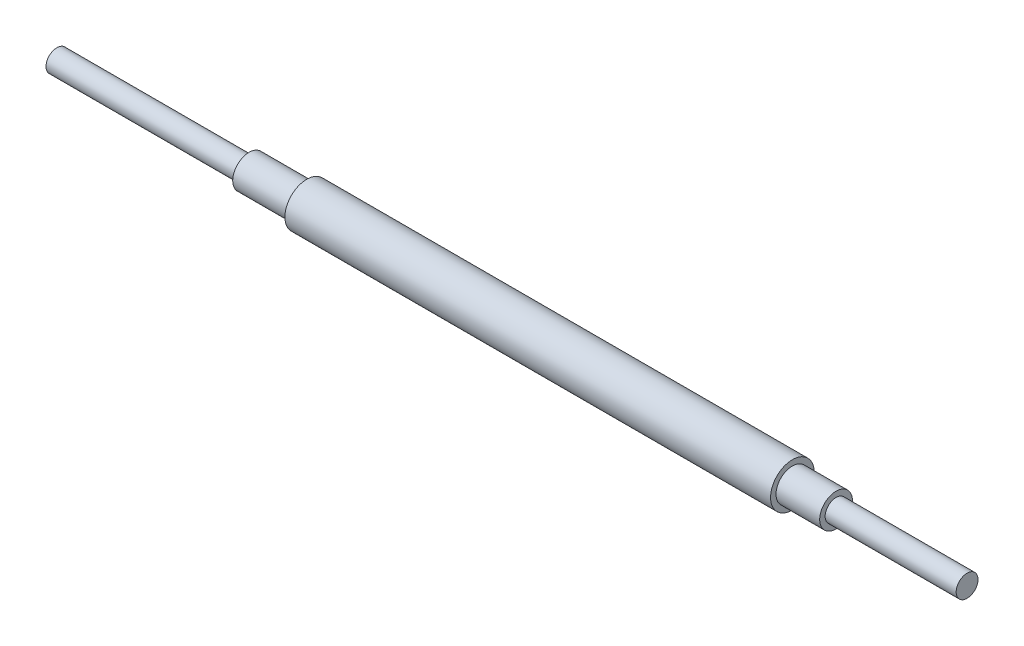
SolidWorks part; units mm, degrees
ref_plane "Front Plane" through (0, 0, 0) normal (0, 0, 1) x (1, 0, 0)
ref_plane "Top Plane" through (0, 0, 0) normal (0, 1, 0) x (1, 0, 0)
ref_plane "Right Plane" through (0, 0, 0) normal (1, 0, 0) x (0, 0, -1)
sketch "Sketch1" plane through (0, 0, 0) normal (0, 0, 1) x (1, 0, 0)
  line L3 (0.6124, 3.175) -> (0.6124, 0)
  line L4 (0.6124, 3.175) -> (-37.4876, 3.175)
  line L5 (-37.4876, 3.175) -> (-37.4876, 4.7625)
  line L6 (-37.4876, 4.7625) -> (-50.1876, 4.7625)
  line L7 (-50.1876, 4.7625) -> (-50.1876, 6.35)
  line L8 (-50.1876, 6.35) -> (-191.4116, 6.35)
  line L9 (-191.4116, 6.35) -> (-191.4116, 4.7625)
  line L10 (-191.4116, 4.7625) -> (-208.1756, 4.7625)
  line L11 (-208.1756, 4.7625) -> (-208.1756, 3.175)
  line L12 (-208.1756, 3.175) -> (-264.0556, 3.175)
  line L13 (-264.0556, 3.175) -> (-264.0556, 0)
  line L14 (-264.0556, 0) -> (0.6124, 0)
  line L16 (-191.4116, -5.0403) -> (-191.4116, 5.0403) construction
  line L18 (0, 0) -> (27.519, 0) construction
  line L19 (-258.9756, 10.16) -> (-258.9756, -10.16) construction
  dimension "D1" = 6.35
  dimension "D3" = 4.7625
  dimension "D4" = 3.175
  dimension ".35" = 38.1
  dimension "D6" = 3.175
  dimension "D7" = 141.224
  dimension "D9" = 5.08
  dimension "D2" = 12.7
  dimension "D5" = 16.764
revolve "Revolve1" add sketch "Sketch1" angle 360 about L14
equation "\"CompressorInnerDiameter\"=0.125"
equation "\"D4@Sketch1\"=\"CompressorInnerDiameter\""
